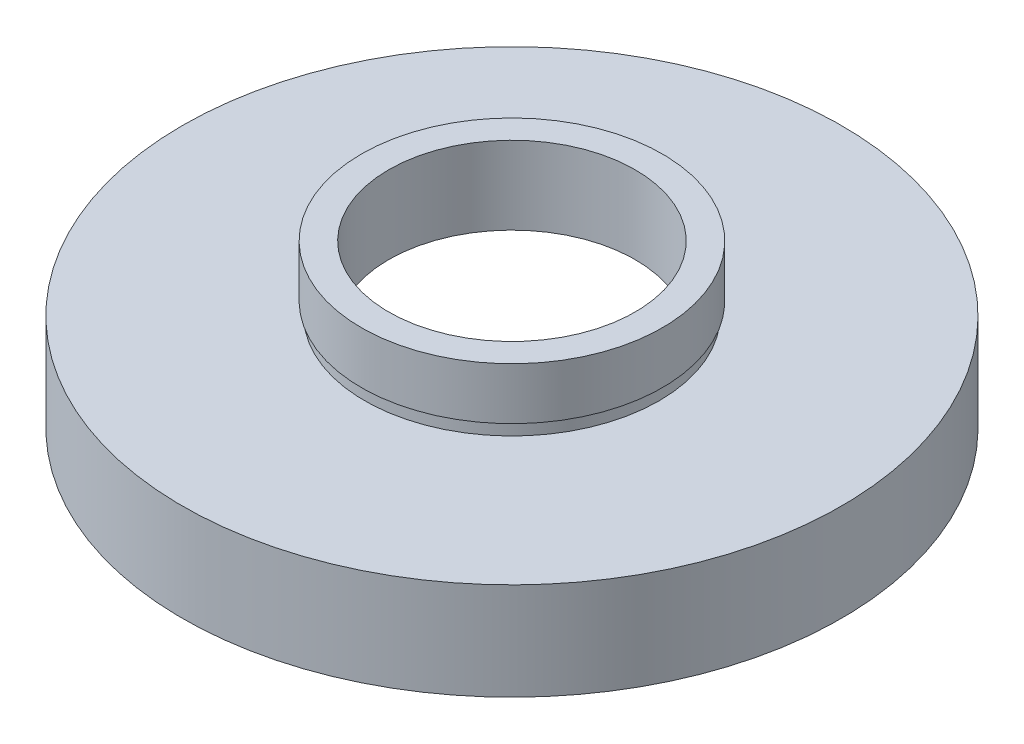
SolidWorks part; units mm, degrees
ref_plane "前视基准面" through (0, 0, 0) normal (0, 0, 1) x (1, 0, 0)
ref_plane "上视基准面" through (0, 0, 0) normal (0, 1, 0) x (1, 0, 0)
ref_plane "右视基准面" through (0, 0, 0) normal (1, 0, 0) x (0, 0, -1)
sketch "草图1" plane through (0, 0, 0) normal (0, 0, 1) x (1, 0, 0)
  line L0 (0, 16.886) -> (0, -24.4878) construction
  line L1 (20.5, 0) -> (20.5, 5.5)
  line L2 (9.5, 6.5) -> (21.1, 6.5)
  line L3 (9.5, 6.5) -> (9.5, 12.5)
  line L4 (9.5, 12.5) -> (11.6, 12.5)
  line L5 (11.6, 12.5) -> (11.6, 8.5)
  line L6 (11.6, 8.5) -> (11.35, 8.5)
  line L7 (11.35, 8.5) -> (11.35, 7.5)
  line L8 (11.35, 7.5) -> (25.4, 7.5)
  line L9 (25.4, 7.5) -> (25.4, 0)
  line L10 (25.4, 0) -> (20.5, 0)
  line L11 (20.5, 5.5) -> (21.1, 5.5)
  line L12 (21.1, 5.5) -> (21.1, 6.5)
  line L13 (0, 0) -> (3.4668, 0) construction
  point P4 (22.95, 0)
  dimension "D1" = 9.5
  dimension "D2" = 11.6
  dimension "D3" = 11.35
  dimension "D4" = 20.5
  dimension "D5" = 21.1
  dimension "D6" = 25.4
  dimension "D7" = 12.5
  dimension "D8" = 7.5
  dimension "D9" = 1
  dimension "D10" = 5.5
  dimension "D11" = 1
revolve "旋转1" add sketch "草图1" angle 360 about L0
cosmetic thread "装饰螺纹线1" parameters "D2"=22.2
cosmetic thread "装饰螺纹线2" parameters "D2"=20
cosmetic thread "装饰螺纹线3" parameters "D2"=42
